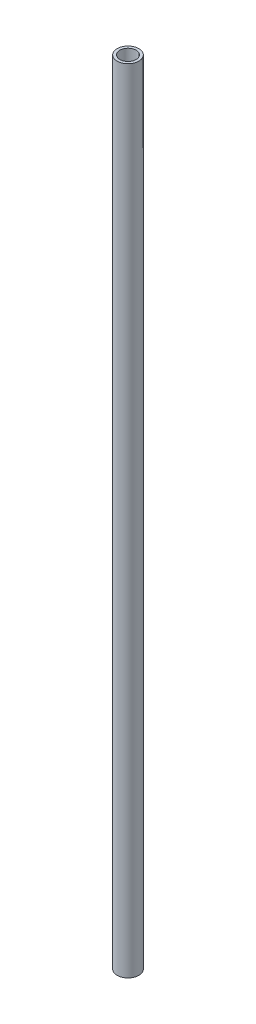
SolidWorks part; units mm, degrees
material "AISI Type 316L stainless steel"
ref_plane "Front Plane" through (0, 0, 0) normal (0, 0, 1) x (1, 0, 0)
ref_plane "Top Plane" through (0, 0, 0) normal (0, 1, 0) x (1, 0, 0)
ref_plane "Right Plane" through (0, 0, 0) normal (1, 0, 0) x (0, 0, -1)
sketch "Sketch1" plane through (0, 0, 0) normal (0, 1, 0) x (1, 0, 0)
  circle A0 centre (0, 0) radius 12.7
  circle A1 centre (0, 0) radius 9.525
  dimension "D1" = 19.05
  dimension "D2" = 25.4
extrude "Boss-Extrude1" add sketch "Sketch1" along normal mid plane 927.1
